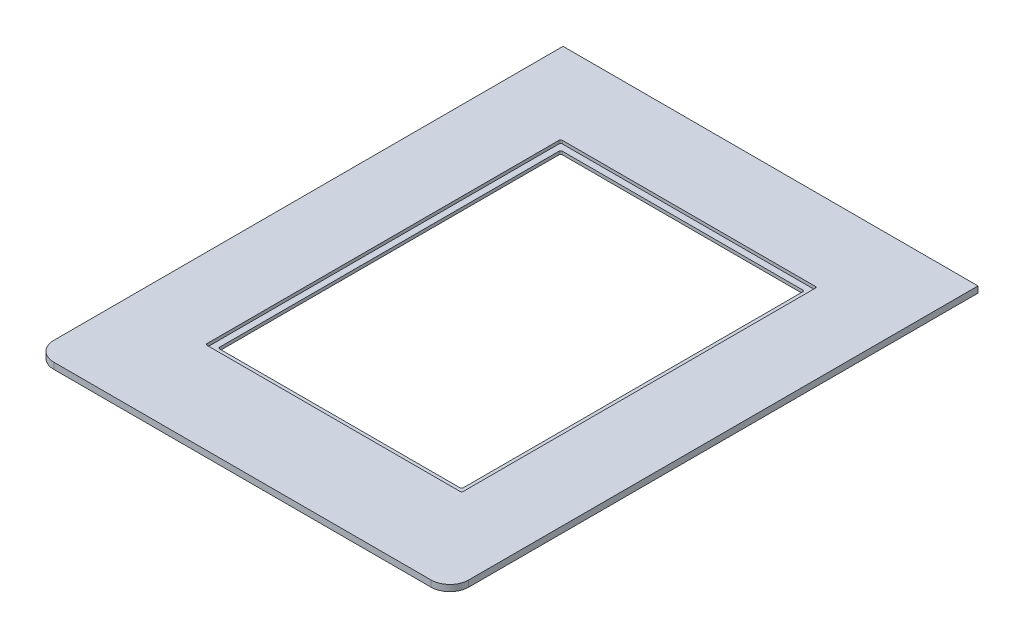
SolidWorks part; units mm, degrees
material "6061 Alloy"
ref_plane "Front Plane" through (0, 0, 0) normal (0, 0, 1) x (1, 0, 0)
ref_plane "Top Plane" through (0, 0, 0) normal (0, 1, 0) x (1, 0, 0)
ref_plane "Right Plane" through (0, 0, 0) normal (1, 0, 0) x (0, 0, -1)
sketch "Sketch1" plane through (0, 0, 0) normal (0, 1, 0) x (1, 0, 0)
  line L0 (209.55, 533.4) -> (209.55, 444.5) construction
  line L1 (0, 0) -> (419.1, 0)
  line L2 (0, 0) -> (0, 533.4)
  line L3 (0, 533.4) -> (419.1, 533.4)
  line L4 (419.1, 0) -> (419.1, 533.4)
  line L5 (86.5187, 444.5) -> (332.5812, 444.5)
  line L6 (86.5187, 444.5) -> (86.5187, 98.425)
  line L7 (86.5187, 98.425) -> (332.5813, 98.425)
  line L8 (332.5812, 444.5) -> (332.5813, 98.425)
  dimension "D1" = 246.0625
  dimension "D2" = 346.075
  dimension "D3" = 88.9
  dimension "D4" = 533.4
  dimension "D5" = 419.1
extrude "Overall shape" add sketch "Sketch1" along normal blind 6.35
sketch "Sketch4" plane through (0, 6.35, 0) normal (0, 1, 0) x (1, 0, 0)
  line L0 (0, 533.4) -> (0, 0) construction
  line L1 (419.1, 533.4) -> (0, 533.4) construction
  line L2 (209.55, 533.4) -> (209.55, 0) construction
  line L3 (0, 0) -> (419.1, 0) construction
  line L4 (0, 266.7) -> (419.1, 266.7) construction
  line L5 (419.1, 0) -> (419.1, 533.4) construction
  circle A0 centre (50.8, 482.6) radius 2.54
  circle A1 centre (368.3, 482.6) radius 2.54
  circle A2 centre (368.3, 50.8) radius 2.54
  circle A3 centre (50.8, 50.8) radius 2.54
  dimension "D1" = 5.08
  dimension "D2" = 50.8
  dimension "D3" = 50.8
extrude "Rubber foot holes" [suppressed] cut sketch "Sketch4" against normal through all
sketch "Sketch5" plane through (0, 6.35, 0) normal (0, 1, 0) x (1, 0, 0)
  line L14 (80.1688, 92.075) -> (338.9313, 92.075)
  line L15 (338.9313, 92.075) -> (338.9312, 450.85)
  line L16 (80.1687, 450.85) -> (80.1688, 92.075)
  line L17 (338.9312, 450.85) -> (80.1687, 450.85)
  line L18 (80.1688, 92.075) -> (338.9313, 92.075)
  line L19 (338.9313, 92.075) -> (338.9312, 450.85)
  line L20 (80.1687, 450.85) -> (80.1688, 92.075)
  line L21 (338.9312, 450.85) -> (80.1687, 450.85)
  dimension "D1" = 6.35
extrude "Glass inset cut" cut sketch "Sketch5" against normal blind 3.175
fillet "Glass inset fillets" radius 1.5875 8 edges at (338.9313, 4.7625, -92.075) (80.1688, 4.7625, -92.075) (338.9312, 4.7625, -450.85) (80.1687, 4.7625, -450.85) (86.5187, 1.5875, -98.425) (332.5813, 1.5875, -98.425) (332.5812, 1.5875, -444.5) (86.5187, 1.5875, -444.5)
ref_plane "Center plane" through (209.55, 0, 0) normal (1, 0, 0) x (0, 0, -1)
sketch "Sketch8" plane through (0, 6.35, 0) normal (0, 1, 0) x (1, 0, 0)
  line L0 (209.55, 533.4) -> (209.55, 0) construction
  line L1 (209.55, -3.4925) -> (209.55, 3.4925) construction
  line L2 (190.3286, 0) -> (190.3286, 533.4) construction
  line L3 (0, 0) -> (419.1, 0) construction
  line L4 (419.1, 533.4) -> (0, 533.4) construction
  line L5 (228.7715, 0) -> (228.7715, 533.4) construction
  line L6 (190.3285, 100.1522) -> (198.1517, 100.1522) construction
  line L7 (198.1517, 100.1522) -> (198.1517, 49.4665) construction
  line L8 (228.7715, 106.6546) -> (220.9483, 106.6546) construction
  line L9 (220.9483, 106.6546) -> (220.9483, 57.6072) construction
  line L10 (190.3286, 426.7454) -> (198.1518, 426.7454) construction
  line L11 (198.1518, 426.7454) -> (198.1518, 475.7928) construction
  line L12 (228.7715, 433.2478) -> (220.9483, 433.2478) construction
  line L13 (220.9483, 433.2478) -> (220.9483, 483.9335) construction
  circle A0 centre (198.1517, 100.1522) radius 1.9177
  circle A1 centre (220.9483, 106.6546) radius 1.9177
  circle A2 centre (198.1517, 49.4665) radius 1.9177
  circle A3 centre (220.9483, 57.6072) radius 1.9177
  circle A4 centre (198.1518, 426.7454) radius 1.9177 construction
  circle A5 centre (220.9483, 433.2478) radius 1.9177 construction
  circle A6 centre (198.1518, 475.7928) radius 1.9177
  circle A7 centre (220.9483, 483.9335) radius 1.9177
  point P22 (209.55, 266.7)
  point P34 (254, 342.9)
  dimension "D3" = 7.8232
  dimension "D4" = 3.8354
  dimension "D9" = 3.8354
  dimension "D1" = 19.2215
  dimension "D2" = 19.2215
  dimension "D5" = 49.4665
  dimension "D6" = 57.6072
  dimension "D7" = 100.1522
  dimension "D8" = 106.6546
  dimension "D10" = 7.8232
  dimension "D11" = 106.6546
  dimension "D12" = 100.1522
  dimension "D13" = 57.6072
  dimension "D14" = 49.4665
extrude "Y axis bracket holes" [suppressed] cut sketch "Sketch8" against normal through all
sketch "Sketch9" plane through (0, 6.35, 0) normal (0, 1, 0) x (1, 0, 0)
  line L0 (22.6314, 533.4) -> (22.6314, 0) construction
  line L1 (419.1, 533.4) -> (0, 533.4) construction
  line L2 (0, 0) -> (419.1, 0) construction
  line L3 (0, 533.4) -> (0, 0) construction
  line L4 (209.55, 474.7828) -> (209.55, -49525.2172) construction
  line L5 (209.55, -3.4925) -> (209.55, 3.4925) construction
  line L6 (22.6314, 179.3875) -> (22.6314, 533.4) construction
  circle A0 centre (396.4686, 198.5772) radius 2.2225
  circle A1 centre (396.4686, 259.7785) radius 2.2225
  circle A2 centre (396.4686, 498.602) radius 3.175
  circle A3 centre (22.6314, 498.602) radius 3.175
  circle A4 centre (22.6314, 259.7785) radius 2.2225
  circle A5 centre (22.6314, 198.5772) radius 2.2225
  dimension "D6" = 4.445
  dimension "D7" = 4.445
  dimension "D3" = 6.35
  dimension "D1" = 22.6314
  dimension "D2" = 34.798
  dimension "D4" = 19.1897
  dimension "D5" = 80.391
  dimension "D8" = 354.0125
extrude "Y axis slide holes" [suppressed] cut sketch "Sketch9" against normal through all
fillet "Fillet1" radius 19.05 2 edges at (419.1, 3.175, 0) (0, 3.175, 0)
equation "\"glass pane length\" = 14.125"
equation "\"glass pane width\" = 10.1875"
equation "\"D1@Sketch1\"=\"glass pane width\"-\"glass lip\"*2"
equation "\"D2@Sketch1\"=\"glass pane length\"-\"glass lip\"*2"
equation "\"glass pane wall width\" = 3/4"
equation "\"glass lip\" = 1/4"
equation "\"bolt diameter\" = 0.2"
equation "\"stepper body width\" = 2.22"
equation "\"stepper mount offset\" = 0.19"
equation "\"stepper mount diameter\" = 0.19"
equation "\"thin metal\" = 0.12"
equation "\"thick metal\" = 0.25"
equation "\"D1@Overall shape\" = \"thick metal\""
equation "\"y axis stepper wall bracket thickness\" = 1"
equation "\"y axis stepper wall mount side offset\" = 1/2"
equation "\"y axis stepper wall mount top offset\" = 1/2"
equation "\"stepper shaft offset from body\" = 0.79"
equation "\"stepper spacer thickness\" = 0.2"
equation "\"y axis stepper wall height off base\" = 8"
equation "\"D4@Sketch1\" = \"base length\""
equation "\"base length\" = 21"
equation "\"D1@Sketch5\"=\"glass lip\""
equation "\"D1@Glass inset cut\" = 0.125"
equation "\"recognizer width\" = 2.4"
equation "\"y axis stepper wall width\" = \"stepper body width\" + 1                  "
equation "\"base width\" = 16.5"
equation "\"D5@Sketch1\" = \"base width\""
equation "\"D5@Sketch8\"=1.8275+\"thin metal\""
equation "\"D8@Sketch8\"=4.079+\"thin metal\""
equation "\"D6@Sketch8\"=2.148+\"thin metal\""
equation "\"D11@Sketch8\"=4.079+\"thin metal\""
equation "\"D12@Sketch8\"=3.823+\"thin metal\""
equation "\"D13@Sketch8\"=2.148+\"thin metal\""
equation "\"D14@Sketch8\"=1.8275+\"thin metal\""
equation "\"D1@Sketch9\"=1.782/2"
equation "\"D7@Sketch8\"=3.823+\"thin metal\""
